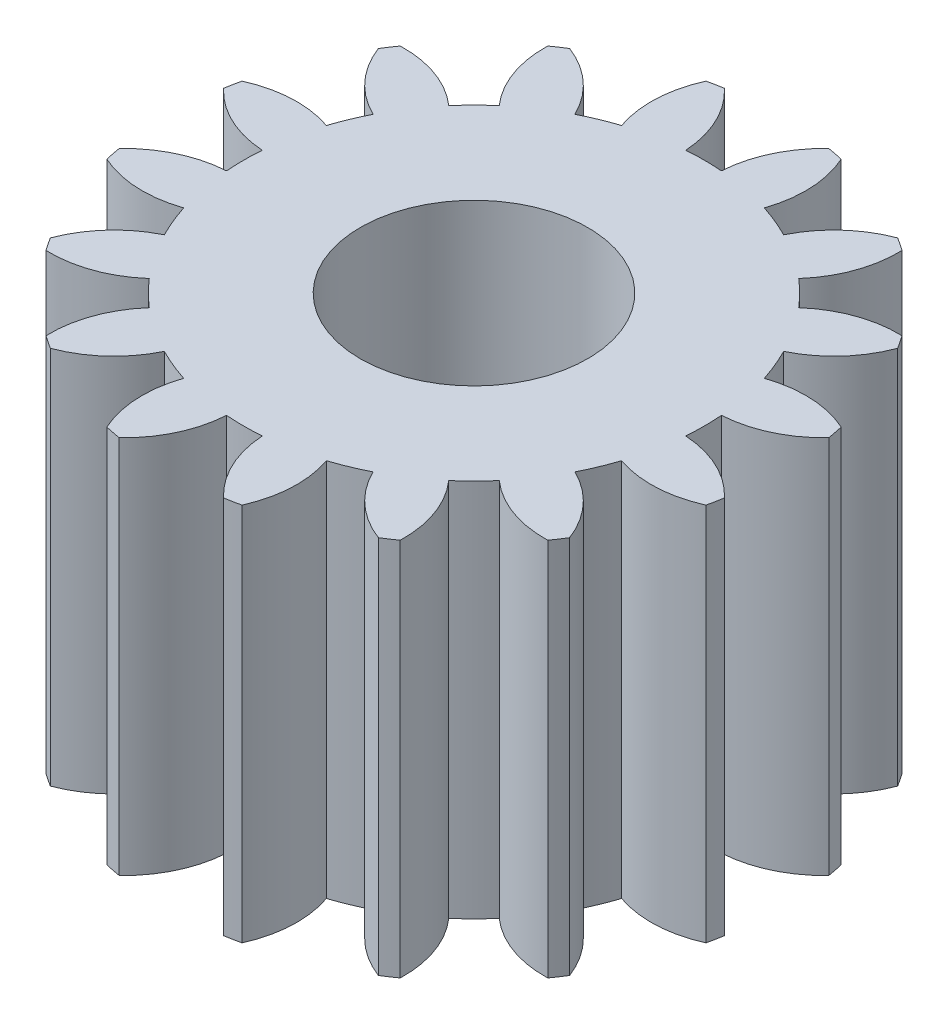
SolidWorks part; units mm, degrees
ref_plane "Front Plane" through (0, 0, 0) normal (0, 0, 1) x (1, 0, 0)
ref_plane "Top Plane" through (0, 0, 0) normal (0, 1, 0) x (1, 0, 0)
ref_plane "Right Plane" through (0, 0, 0) normal (1, 0, 0) x (0, 0, -1)
sketch "Sketch1" plane through (0, 0, 0) normal (0, 1, 0) x (1, 0, 0)
  arc A0 (-7.9822, 1.3766) -> (-6.0557, 0.4711) centre (-5.8806, 3.3458) ccw
  arc A1 (-6.0557, 0.4711) -> (-6.0557, -0.4711) centre (0, 0) ccw
  arc A2 (-6.0557, -0.4711) -> (-7.9822, -1.3766) centre (-5.8806, -3.3458) ccw
  arc A3 (-7.9822, -1.3766) -> (-7.9014, -1.7829) centre (0, 0) ccw
  arc A4 (-7.9014, -1.7829) -> (-5.775, -1.8822) centre (-6.7134, 0.8407) ccw
  arc A5 (-5.775, -1.8822) -> (-5.4145, -2.7527) centre (0, 0) ccw
  arc A6 (-5.4145, -2.7527) -> (-6.8478, -4.3264) centre (-4.1526, -5.3415) ccw
  arc A7 (-6.8478, -4.3264) -> (-6.6176, -4.6709) centre (0, 0) ccw
  arc A8 (-6.6176, -4.6709) -> (-4.6152, -3.9489) centre (-6.524, -1.7924) ccw
  arc A9 (-4.6152, -3.9489) -> (-3.9489, -4.6152) centre (0, 0) ccw
  arc A10 (-3.9489, -4.6152) -> (-4.6709, -6.6176) centre (-1.7924, -6.524) ccw
  arc A11 (-4.6709, -6.6176) -> (-4.3264, -6.8478) centre (0, 0) ccw
  arc A12 (-4.3264, -6.8478) -> (-2.7527, -5.4145) centre (-5.3415, -4.1526) ccw
  arc A13 (-2.7527, -5.4145) -> (-1.8822, -5.775) centre (0, 0) ccw
  arc A14 (-1.8822, -5.775) -> (-1.7829, -7.9014) centre (0.8407, -6.7134) ccw
  arc A15 (-1.7829, -7.9014) -> (-1.3766, -7.9822) centre (0, 0) ccw
  arc A16 (-1.3766, -7.9822) -> (-0.4711, -6.0557) centre (-3.3458, -5.8806) ccw
  arc A17 (-0.4711, -6.0557) -> (0.4711, -6.0557) centre (0, 0) ccw
  arc A18 (0.4711, -6.0557) -> (1.3766, -7.9822) centre (3.3458, -5.8806) ccw
  arc A19 (1.3766, -7.9822) -> (1.7829, -7.9014) centre (0, 0) ccw
  arc A20 (1.7829, -7.9014) -> (1.8822, -5.775) centre (-0.8407, -6.7134) ccw
  arc A21 (1.8822, -5.775) -> (2.7527, -5.4145) centre (0, 0) ccw
  arc A22 (2.7527, -5.4145) -> (4.3264, -6.8478) centre (5.3415, -4.1526) ccw
  arc A23 (4.3264, -6.8478) -> (4.6709, -6.6176) centre (0, 0) ccw
  arc A24 (4.6709, -6.6176) -> (3.9489, -4.6152) centre (1.7924, -6.524) ccw
  arc A25 (3.9489, -4.6152) -> (4.6152, -3.9489) centre (0, 0) ccw
  arc A26 (4.6152, -3.9489) -> (6.6176, -4.6709) centre (6.524, -1.7924) ccw
  arc A27 (6.6176, -4.6709) -> (6.8478, -4.3264) centre (0, 0) ccw
  arc A28 (6.8478, -4.3264) -> (5.4145, -2.7527) centre (4.1526, -5.3415) ccw
  arc A29 (5.4145, -2.7527) -> (5.775, -1.8822) centre (0, 0) ccw
  arc A30 (5.775, -1.8822) -> (7.9014, -1.7829) centre (6.7134, 0.8407) ccw
  arc A31 (7.9014, -1.7829) -> (7.9822, -1.3766) centre (0, 0) ccw
  arc A32 (7.9822, -1.3766) -> (6.0557, -0.4711) centre (5.8806, -3.3458) ccw
  arc A33 (6.0557, -0.4711) -> (6.0557, 0.4711) centre (0, 0) ccw
  arc A34 (6.0557, 0.4711) -> (7.9822, 1.3766) centre (5.8806, 3.3458) ccw
  arc A35 (7.9822, 1.3766) -> (7.9014, 1.7829) centre (0, 0) ccw
  arc A36 (7.9014, 1.7829) -> (5.775, 1.8822) centre (6.7134, -0.8407) ccw
  arc A37 (5.775, 1.8822) -> (5.4145, 2.7527) centre (0, 0) ccw
  arc A38 (5.4145, 2.7527) -> (6.8478, 4.3264) centre (4.1526, 5.3415) ccw
  arc A39 (6.8478, 4.3264) -> (6.6176, 4.6709) centre (0, 0) ccw
  arc A40 (6.6176, 4.6709) -> (4.6152, 3.9489) centre (6.524, 1.7924) ccw
  arc A41 (4.6152, 3.9489) -> (3.9489, 4.6152) centre (0, 0) ccw
  arc A42 (3.9489, 4.6152) -> (4.6709, 6.6176) centre (1.7924, 6.524) ccw
  arc A43 (4.6709, 6.6176) -> (4.3264, 6.8478) centre (0, 0) ccw
  arc A44 (4.3264, 6.8478) -> (2.7527, 5.4145) centre (5.3415, 4.1526) ccw
  arc A45 (2.7527, 5.4145) -> (1.8822, 5.775) centre (0, 0) ccw
  arc A46 (1.8822, 5.775) -> (1.7829, 7.9014) centre (-0.8407, 6.7134) ccw
  arc A47 (1.7829, 7.9014) -> (1.3766, 7.9822) centre (0, 0) ccw
  arc A48 (1.3766, 7.9822) -> (0.4711, 6.0557) centre (3.3458, 5.8806) ccw
  arc A49 (0.4711, 6.0557) -> (-0.4711, 6.0557) centre (0, 0) ccw
  arc A50 (-0.4711, 6.0557) -> (-1.3766, 7.9822) centre (-3.3458, 5.8806) ccw
  arc A51 (-1.3766, 7.9822) -> (-1.7829, 7.9014) centre (0, 0) ccw
  arc A52 (-1.7829, 7.9014) -> (-1.8822, 5.775) centre (0.8407, 6.7134) ccw
  arc A53 (-1.8822, 5.775) -> (-2.7527, 5.4145) centre (0, 0) ccw
  arc A54 (-2.7527, 5.4145) -> (-4.3264, 6.8478) centre (-5.3415, 4.1526) ccw
  arc A55 (-4.3264, 6.8478) -> (-4.6709, 6.6176) centre (0, 0) ccw
  arc A56 (-4.6709, 6.6176) -> (-3.9489, 4.6152) centre (-1.7924, 6.524) ccw
  arc A57 (-3.9489, 4.6152) -> (-4.6152, 3.9489) centre (0, 0) ccw
  arc A58 (-4.6152, 3.9489) -> (-6.6176, 4.6709) centre (-6.524, 1.7924) ccw
  arc A59 (-6.6176, 4.6709) -> (-6.8478, 4.3264) centre (0, 0) ccw
  arc A60 (-6.8478, 4.3264) -> (-5.4145, 2.7527) centre (-4.1526, 5.3415) ccw
  arc A61 (-5.4145, 2.7527) -> (-5.775, 1.8822) centre (0, 0) ccw
  arc A62 (-5.775, 1.8822) -> (-7.9014, 1.7829) centre (-6.7134, -0.8407) ccw
  arc A63 (-7.9014, 1.7829) -> (-7.9822, 1.3766) centre (0, 0) ccw
extrude "Boss-Extrude1" add sketch "Sketch1" along normal blind 10
sketch "Sketch2" plane through (0, 10, 0) normal (0, 1, 0) x (1, 0, 0)
  circle A0 centre (0, 0) radius 3
  dimension "D1" = 6
extrude "Cut-Extrude1" cut sketch "Sketch2" against normal blind 10
